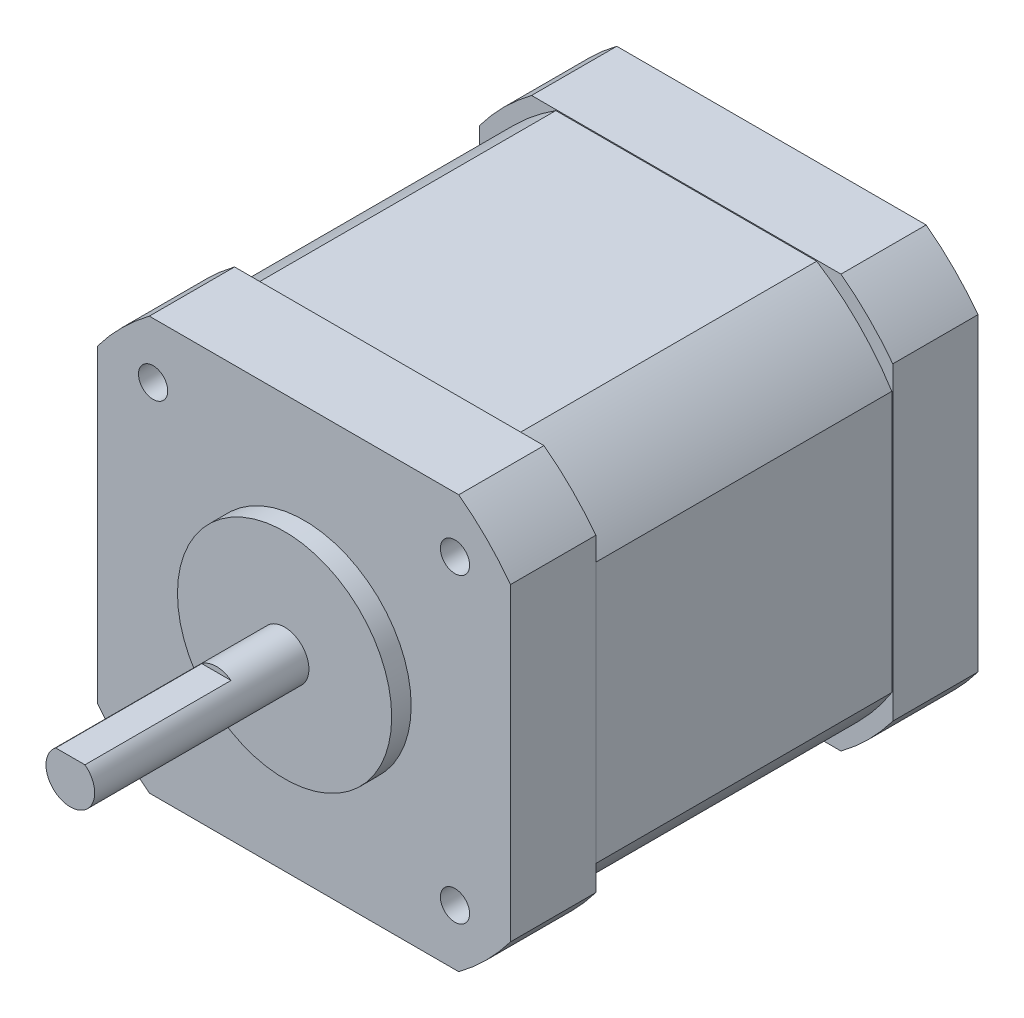
SolidWorks part; units mm, degrees
material "Plain Carbon Steel"
ref_plane "Front" through (0, 0, 0) normal (0, 0, 1) x (1, 0, 0)
ref_plane "Top" through (0, 0, 0) normal (0, 1, 0) x (1, 0, 0)
ref_plane "Right" through (0, 0, 0) normal (1, 0, 0) x (0, 0, -1)
sketch "Sketch1" plane through (0, 0, 0) normal (0, 0, 1) x (1, 0, 0)
  circle A0 centre (0, 0) radius 2.5
  dimension "D1" = 5
extrude "Boss-Extrude1" add sketch "Sketch1" along normal blind 24
sketch "Sketch2" plane through (0, 0, 0) normal (0, 0, -1) x (-1, 0, 0)
  circle A0 centre (0, 0) radius 11
  dimension "D1" = 22
extrude "Boss-Extrude2" add sketch "Sketch2" against normal blind 2
sketch "Sketch3" plane through (0, 0, 0) normal (0, 0, -1) x (-1, 0, 0)
  line L1 (21.209, -21.209) -> (-21.209, -21.209)
  line L2 (21.209, -21.209) -> (21.209, 21.209)
  line L3 (21.209, 21.209) -> (-21.209, 21.209)
  line L4 (-21.209, -21.209) -> (-21.209, 21.209)
  line L5 (21.209, -21.209) -> (-21.209, 21.209) construction
  line L6 (21.209, 21.209) -> (-21.209, -21.209) construction
  point P0 (0, 0)
  dimension "D1" = 42.418
extrude "Boss-Extrude3" add sketch "Sketch3" along normal blind 48
sketch "Sketch4" plane through (0, 0, -48) normal (0, 0, -1) x (-1, 0, 0)
  line L0 (-21.209, -15.888) -> (-21.209, -21.209)
  line L1 (15.888, -21.209) -> (21.209, -21.209)
  line L2 (21.209, 15.888) -> (21.209, 21.209)
  line L3 (-15.888, 21.209) -> (-21.209, 21.209)
  line L4 (-21.209, 21.209) -> (-21.209, -21.209)
  line L5 (-21.209, -21.209) -> (21.209, -21.209)
  line L6 (21.209, -21.209) -> (21.209, 21.209)
  line L7 (21.209, 21.209) -> (-21.209, 21.209)
  line L8 (-21.209, 21.209) -> (-21.209, 15.888)
  line L9 (-21.209, -21.209) -> (-15.888, -21.209)
  line L10 (21.209, -21.209) -> (21.209, -15.888)
  line L11 (21.209, 21.209) -> (15.888, 21.209)
  arc A0 (-21.209, -15.888) -> (-15.888, -21.209) centre (0, 0) ccw
  arc A1 (15.888, -21.209) -> (21.209, -15.888) centre (0, 0) ccw
  arc A2 (21.209, 15.888) -> (15.888, 21.209) centre (0, 0) ccw
  arc A3 (-15.888, 21.209) -> (-21.209, 15.888) centre (0, 0) ccw
  dimension "D2" = 26.5
  dimension "D1" = 0
extrude "Cut-Extrude1" cut sketch "Sketch4" against normal through all
hole_wizard "M3x0.5 Tapped Hole1" positions "Sketch6" profile "Sketch5" tap size "M3x0.5" standard "ANSI Metric"
sketch "Sketch6" plane through (0, 0, 0) normal (0, 0, 1) x (1, 0, 0)
  line L0 (-16.1632, 0) -> (0, 0) construction
  line L1 (0, 0) -> (0, 15.0764) construction
  point P0 (-15.5, 15.5)
  point P11 (-15.5, -15.5)
  point P12 (15.5, -15.5)
  point P13 (15.5, 15.5)
  dimension "D1" = 31
  dimension "D2" = 31
sketch "Sketch5" plane through (-15.5, 15.5, 0) normal (1, 0, 0) x (0, -1, 0)
  line L0 (0, 0) -> (0, 5.2511)
  line L1 (0, 5.2511) -> (1.25, 4.5)
  line L2 (1.25, 4.5) -> (1.25, 6)
  line L3 (1.25, 6) -> (1.5, 6)
  line L4 (1.5, 6) -> (1.5, 0)
  line L5 (1.5, 0) -> (0, 0)
  line L10 (0, 5.2511) -> (-1.25, 4.5) construction
  line L11 (0, -6.35) -> (0, 107.95) construction
  dimension "Tap Drill Dia." = 2.5
  dimension "Tap Drill Depth" = 4.5
  dimension "Thread Major Dia." = 3
  dimension "Thread Depth" = 6
  dimension "Drill Angle" = 118
sketch "Sketch7" plane through (0, 0, 24) normal (0, 0, 1) x (1, 0, 0)
  line L0 (-1.5, 2) -> (1.5, 2)
  circle A0 centre (0, 0) radius 2.5 construction
  circle A1 centre (0, 0) radius 2.5 construction
  arc A2 (1.5, 2) -> (-1.5, 2) centre (0, 0) ccw
  dimension "D1" = 4.5
extrude "Cut-Extrude2" cut sketch "Sketch7" against normal blind 15
ref_plane "Plane1" through (0, 0, -24) normal (0, 0, 1) x (1, 0, 0)
sketch "Sketch8" plane through (0, 0, -24) normal (0, 0, 1) x (1, 0, 0)
  line L0 (-13.3944, 21.109) -> (13.3944, 21.109)
  line L1 (-5.7152, 0) -> (0, 0) construction
  line L2 (0, 0) -> (0, 8.4579) construction
  line L3 (-15.888, 21.209) -> (15.888, 21.209) construction
  line L4 (-13.3944, -21.109) -> (13.3944, -21.109)
  line L5 (-21.109, 13.3944) -> (-21.109, -13.3944)
  line L6 (-21.209, -15.888) -> (-21.209, 15.888) construction
  line L7 (21.109, 13.3944) -> (21.109, -13.3944)
  line L12 (15.888, 21.209) -> (-15.888, 21.209)
  line L13 (-21.209, 15.888) -> (-21.209, -15.888)
  line L14 (-15.888, -21.209) -> (15.888, -21.209)
  line L15 (21.209, -15.888) -> (21.209, 15.888)
  line L16 (15.888, 21.209) -> (-15.888, 21.209)
  line L17 (-21.209, 15.888) -> (-21.209, -15.888)
  line L18 (-15.888, -21.209) -> (15.888, -21.209)
  line L19 (21.209, -15.888) -> (21.209, 15.888)
  arc A0 (-13.3944, 21.109) -> (-21.109, 13.3944) centre (0, 0) ccw
  arc A1 (-21.109, -13.3944) -> (-13.3944, -21.109) centre (0, 0) ccw
  arc A2 (21.109, 13.3944) -> (13.3944, 21.109) centre (0, 0) ccw
  arc A3 (13.3944, -21.109) -> (21.109, -13.3944) centre (0, 0) ccw
  arc A5 (-15.888, 21.209) -> (-21.209, 15.888) centre (0, 0) ccw
  arc A6 (-21.209, -15.888) -> (-15.888, -21.209) centre (0, 0) ccw
  arc A7 (15.888, -21.209) -> (21.209, -15.888) centre (0, 0) ccw
  arc A8 (21.209, 15.888) -> (15.888, 21.209) centre (0, 0) ccw
  arc A9 (-15.888, 21.209) -> (-21.209, 15.888) centre (0, 0) ccw
  arc A10 (-21.209, -15.888) -> (-15.888, -21.209) centre (0, 0) ccw
  arc A11 (15.888, -21.209) -> (21.209, -15.888) centre (0, 0) ccw
  arc A12 (21.209, 15.888) -> (15.888, 21.209) centre (0, 0) ccw
  dimension "D1" = 50
  dimension "D2" = 0.1
  dimension "D3" = 0.1
  dimension "D4" = 0
extrude "Cut-Extrude3" cut sketch "Sketch8" against normal offset from surface 8.75 and the other way offset from surface (15.25 mm away) 8.75 up to face at (0, 0, -48) other way up to face at (-14, 15.5, 0)
